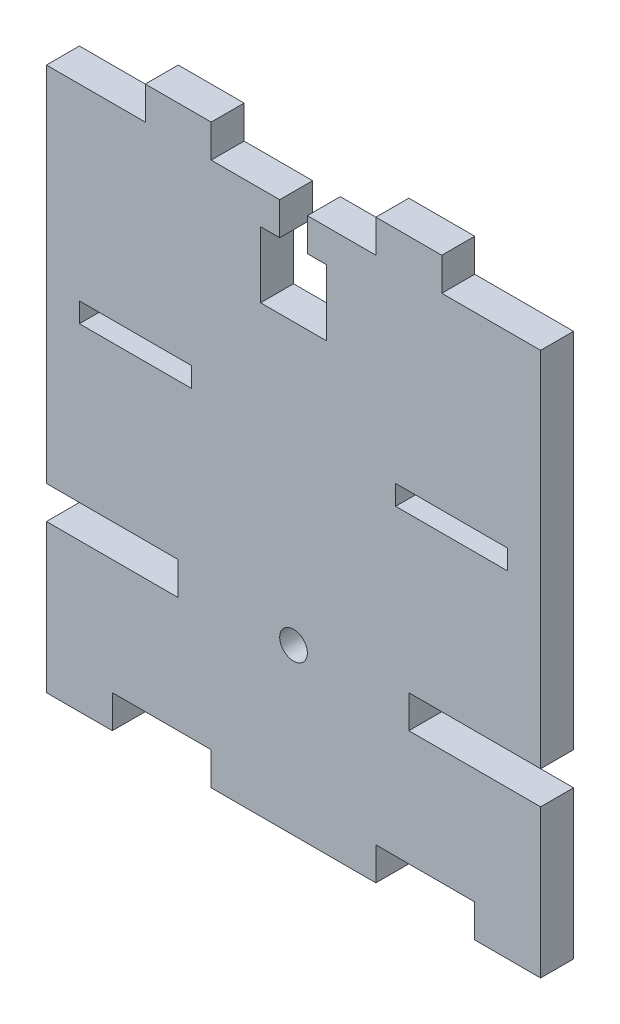
SolidWorks part; units mm, degrees
ref_plane "Front Plane" through (0, 0, 0) normal (0, 0, 1) x (1, 0, 0)
ref_plane "Top Plane" through (0, 0, 0) normal (0, 1, 0) x (1, 0, 0)
ref_plane "Right Plane" through (0, 0, 0) normal (1, 0, 0) x (0, 0, -1)
sketch "Sketch1" plane through (0, 0, 0) normal (0, 0, 1) x (1, 0, 0)
  line L0 (37.5, 17.5) -> (37.5, 10.3798) construction
  line L1 (0, 0) -> (75, 0)
  line L2 (0, 0) -> (0, 17.5)
  line L3 (0, 17.5) -> (75, 17.5)
  line L4 (75, 0) -> (75, 17.5)
  line L9 (20, 17.5) -> (55, 17.5)
  line L10 (20, 17.5) -> (20, 22.5)
  line L11 (20, 22.5) -> (55, 22.5)
  line L12 (55, 17.5) -> (55, 22.5)
  line L17 (0, 8.75) -> (10, 8.75) construction
  line L18 (75, 0) -> (65, 0)
  line L19 (65, 0) -> (65, -5)
  line L20 (75, -5) -> (65, -5)
  line L21 (75, 0) -> (75, -5)
  line L22 (25, -5) -> (50, -5)
  line L23 (50, 0) -> (50, -5)
  line L24 (25, 0) -> (50, 0)
  line L25 (25, 0) -> (25, -5)
  line L26 (0, -5) -> (10, -5)
  line L27 (10, 0) -> (10, -5)
  line L28 (0, 0) -> (10, 0)
  line L29 (0, 0) -> (0, -5)
  circle A0 centre (37.5, 20) radius 2.1
  arc A2 (33.1699, 22.5) -> (41.8301, 22.5) centre (37.5, 20) cw
  point P15 (37.5, -5)
  dimension "D8" = 4.2
  dimension "D9" = 2.5
  dimension "D10" = 5
  dimension "D1" = 17.5
  dimension "D2" = 75
  dimension "D3" = 17.5
  dimension "D4" = 25
  dimension "D5" = 35
  dimension "D6" = 5
extrude "Boss-Extrude1" add sketch "Sketch1" along normal blind 5
sketch "Sketch2" plane through (0, 0, 0) normal (0, 0, -1) x (-1, 0, 0)
  line L1 (0, 22.5) -> (-75, 22.5)
  line L2 (0, 22.5) -> (0, 77.5)
  line L3 (0, 77.5) -> (-75, 77.5)
  line L4 (-75, 22.5) -> (-75, 77.5)
  arc A0 (-33.1699, 22.5) -> (-41.8301, 22.5) centre (-37.5, 20) ccw construction
  arc A1 (-33.1699, 22.5) -> (-41.8301, 22.5) centre (-37.5, 20) ccw
  dimension "D1" = 55
  dimension "D2" = 75
extrude "Boss-Extrude2" add sketch "Sketch2" against normal blind 5
sketch "Sketch3" plane through (0, 0, 0) normal (0, 0, -1) x (-1, 0, 0)
  line L0 (0, 77.5) -> (-75, 77.5) construction
  line L1 (-50, 77.5) -> (-60, 77.5)
  line L2 (-50, 77.5) -> (-50, 82.5)
  line L3 (-50, 82.5) -> (-60, 82.5)
  line L4 (-60, 77.5) -> (-60, 82.5)
  line L5 (-75, -5) -> (-75, 17.5) construction
  line L6 (-37.5, 77.5) -> (-37.5, 80.368) construction
  line L7 (-15, 77.5) -> (-15, 82.5)
  line L8 (-25, 82.5) -> (-15, 82.5)
  line L9 (-25, 77.5) -> (-25, 82.5)
  line L10 (-25, 77.5) -> (-15, 77.5)
  dimension "D1" = 10
  dimension "D2" = 15
  dimension "D3" = 5
extrude "Boss-Extrude3" add sketch "Sketch3" against normal blind 5
sketch "Sketch4" plane through (0, 0, 0) normal (0, 0, -1) x (-1, 0, 0)
  line L0 (-25, 77.5) -> (-50, 77.5) construction
  line L1 (-39.6, 77.5) -> (-35.4, 77.5)
  line L2 (-39.6, 77.5) -> (-39.6, 67.5)
  line L3 (-39.6, 67.5) -> (-35.4, 67.5)
  line L4 (-35.4, 77.5) -> (-35.4, 67.5)
  line L6 (-34, 69.3) -> (-41, 69.3)
  line L7 (-34, 69.3) -> (-34, 72.5)
  line L8 (-34, 72.5) -> (-41, 72.5)
  line L9 (-41, 69.3) -> (-41, 72.5)
  point P10 (-37.5, 77.5)
  point P11 (-37.5, 67.5)
  point P12 (-37.5, 69.3)
  line M25 (-25, 77.5) -> (-50, 77.5)
  dimension "D1" = 7
  dimension "D2" = 3.2
  dimension "D3" = 4.2
  dimension "D4" = 10
  dimension "D5" = 5
extrude "Cut-Extrude1" cut sketch "Sketch4" against normal blind 5 contours L8 L4 L2 M25 | L4 L8 L2 L6 | L4 L6 L2 L3 | L9 L6 L2 L8 | L7 L8 L4 L6
sketch "Sketch5" plane through (0, 0, 0) normal (0, 0, -1) x (-1, 0, 0)
  line L0 (-39.6, 67.5) -> (-35.4, 67.5) construction
  line L1 (-32.5, 72.5) -> (-42.5, 72.5)
  line L2 (-32.5, 72.5) -> (-32.5, 62.5)
  line L3 (-32.5, 62.5) -> (-42.5, 62.5)
  line L4 (-42.5, 72.5) -> (-42.5, 62.5)
  line L5 (-39.6, 72.5) -> (-41, 72.5) construction
  point P4 (-37.5, 62.5)
  point P7 (-37.5, 67.5)
  dimension "D1" = 10
  dimension "D2" = 10
extrude "Cut-Extrude2" cut sketch "Sketch5" against normal blind 5
sketch "Sketch6" plane through (0, 0, 0) normal (0, 0, -1) x (-1, 0, 0)
  line L1 (-75, 44.5) -> (-43, 44.5)
  line L2 (-5, 44.5) -> (-5, 50.5)
  line L3 (-43, 50.5) -> (-75, 50.5)
  line L4 (-37.5, 20) -> (-37.5, 32.3144) construction
  line L5 (-43, 44.5) -> (-43, 50.5)
  line L6 (-75, 22.5) -> (-75, 77.5) construction
  line L7 (-53, 44.5) -> (-53, 50.5)
  line L8 (-70, 44.5) -> (-70, 50.5)
  line L9 (-75, 44.5) -> (-75, 50.5)
  line L10 (-22, 44.5) -> (-22, 50.5)
  line L11 (0, 44.5) -> (-32, 44.5)
  line L16 (-22, 49) -> (-5, 49)
  line L17 (-32, 44.5) -> (-32, 50.5)
  line L18 (-32, 50.5) -> (0, 50.5)
  line L19 (0, 44.5) -> (0, 50.5)
  line L20 (-5, 46) -> (-5, 49)
  line L21 (-53, 46) -> (-70, 46)
  line L22 (-53, 46) -> (-53, 49)
  line L23 (-53, 49) -> (-70, 49)
  line L24 (-70, 46) -> (-70, 49)
  line L25 (-22, 46) -> (-5, 46)
  line L26 (-22, 46) -> (-22, 49)
  line L27 (-75, -5) -> (-75, 17.5) construction
  line L28 (-75, -5) -> (-65, -5) construction
  point P26 (-53, 47.5)
  point P27 (-53, 47.5)
  dimension "D1" = 10
  dimension "D2" = 5
  dimension "D3" = 3
  dimension "D4" = 6
  dimension "D5" = 22
  dimension "D6" = 37.5
  dimension "D7" = 43
  dimension "D8" = 49.5
extrude "Cut-Extrude3" cut sketch "Sketch6" against normal blind 10 contours L8 L1 L7 L3 | L10 L25 L2 L16
